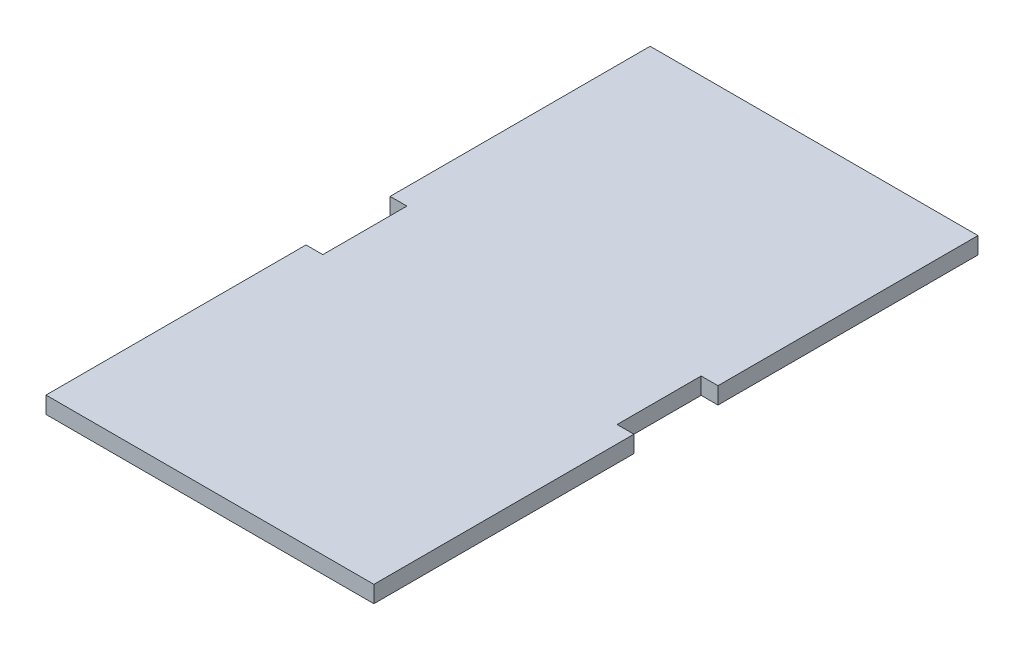
SolidWorks part; units mm, degrees
ref_plane "Front Plane" through (0, 0, 0) normal (0, 0, 1) x (1, 0, 0)
ref_plane "Top Plane" through (0, 0, 0) normal (0, 1, 0) x (1, 0, 0)
ref_plane "Right Plane" through (0, 0, 0) normal (1, 0, 0) x (0, 0, -1)
sketch "Sketch1" plane through (0, 0, 0) normal (0, 1, 0) x (1, 0, 0)
  line L1 (-44.45, 91.2622) -> (44.45, 91.2622)
  line L2 (-44.45, 91.2622) -> (-44.45, -91.2622)
  line L3 (-44.45, -91.2622) -> (44.45, -91.2622)
  line L4 (44.45, 91.2622) -> (44.45, -91.2622)
  line L5 (-44.45, 91.2622) -> (44.45, -91.2622) construction
  line L6 (-44.45, -91.2622) -> (44.45, 91.2622) construction
  line L7 (-44.45, 91.2622) -> (-49.53, 91.2622)
  line L8 (-44.45, 91.2622) -> (-44.45, 12.7)
  line L9 (-44.45, 12.7) -> (-49.53, 12.7)
  line L10 (-49.53, 91.2622) -> (-49.53, 12.7)
  line L11 (-44.45, -91.2622) -> (-49.53, -91.2622)
  line L12 (-44.45, -91.2622) -> (-44.45, -12.7)
  line L13 (-44.45, -12.7) -> (-49.53, -12.7)
  line L14 (-49.53, -91.2622) -> (-49.53, -12.7)
  line L15 (44.45, 91.2622) -> (49.53, 91.2622)
  line L16 (44.45, 91.2622) -> (44.45, 12.7)
  line L17 (44.45, 12.7) -> (49.53, 12.7)
  line L18 (49.53, 91.2622) -> (49.53, 12.7)
  line L19 (44.45, -91.2622) -> (49.53, -91.2622)
  line L20 (44.45, -91.2622) -> (44.45, -12.7)
  line L21 (44.45, -12.7) -> (49.53, -12.7)
  line L22 (49.53, -91.2622) -> (49.53, -12.7)
  point P0 (0, 0)
  dimension "D1" = 88.9
  dimension "D2" = 182.5244
  dimension "D3" = 5.08
  dimension "D4" = 25.4
extrude "Boss-Extrude1" add sketch "Sketch1" along normal blind 5.08 contours L4 L1 L2 L3 | L7 L10 L9 L2 | L14 L11 L2 L13 | L19 L22 L21 L4 | L18 L15 L4 L17
